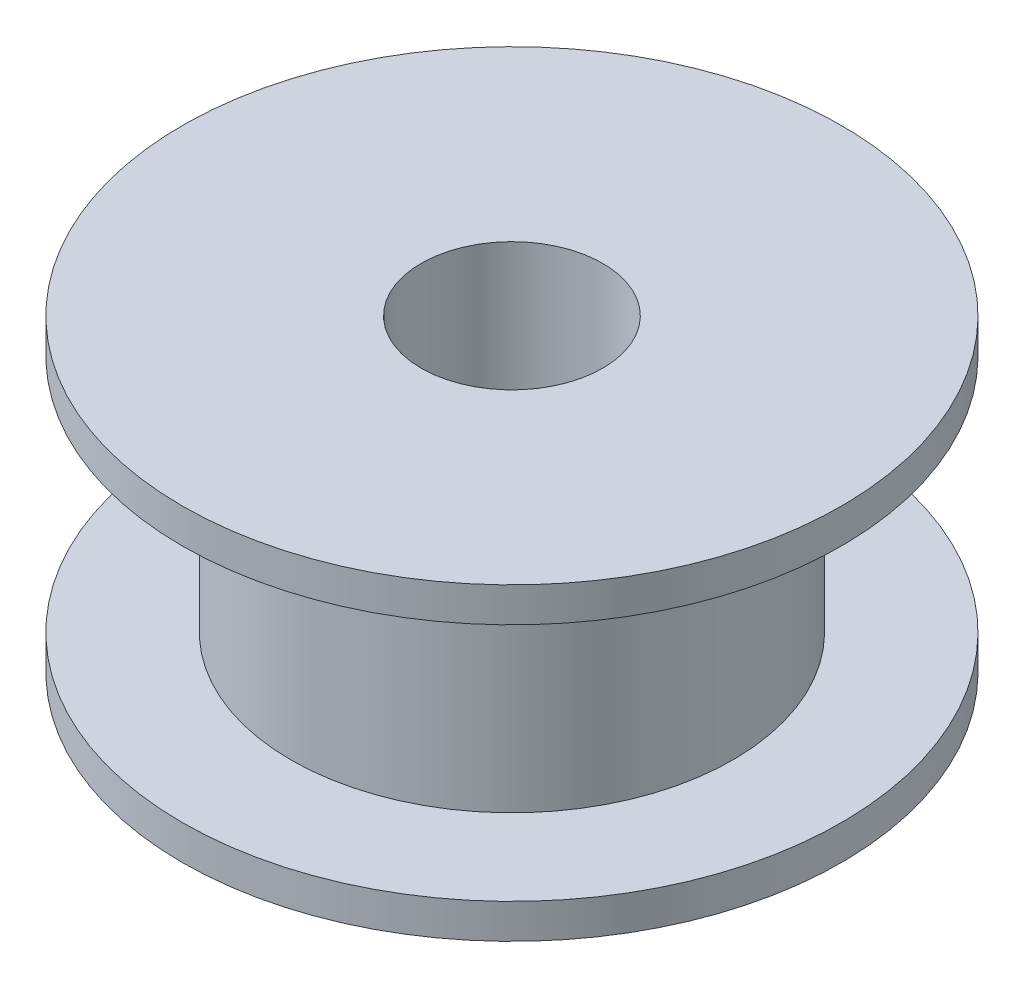
SolidWorks part; units mm, degrees
ref_plane "Front Plane" through (0, 0, 0) normal (0, 0, 1) x (1, 0, 0)
ref_plane "Top Plane" through (0, 0, 0) normal (0, 1, 0) x (1, 0, 0)
ref_plane "Right Plane" through (0, 0, 0) normal (1, 0, 0) x (0, 0, -1)
sketch "Sketch1" plane through (0, 0, 0) normal (0, 1, 0) x (1, 0, 0)
  circle A0 centre (0, 0) radius 8.945
  dimension "D1" = 17.89
extrude "Boss-Extrude1" add sketch "Sketch1" along normal blind 0.94
sketch "Sketch2" plane through (0, 0.94, 0) normal (0, 1, 0) x (1, 0, 0)
  circle A0 centre (0, 0) radius 6
  dimension "D1" = 12
extrude "Boss-Extrude2" add sketch "Sketch2" along normal blind 6.5
sketch "Sketch3" plane through (0, 7.44, 0) normal (0, 1, 0) x (1, 0, 0)
  circle A0 centre (0, 0) radius 8.945
extrude "Boss-Extrude3" add sketch "Sketch3" along normal blind 0.94
sketch "Sketch4" plane through (0, 8.38, 0) normal (0, 1, 0) x (1, 0, 0)
  circle A0 centre (0, 0) radius 2.465
  dimension "D1" = 4.93
extrude "Cut-Extrude1" cut sketch "Sketch4" against normal through all
